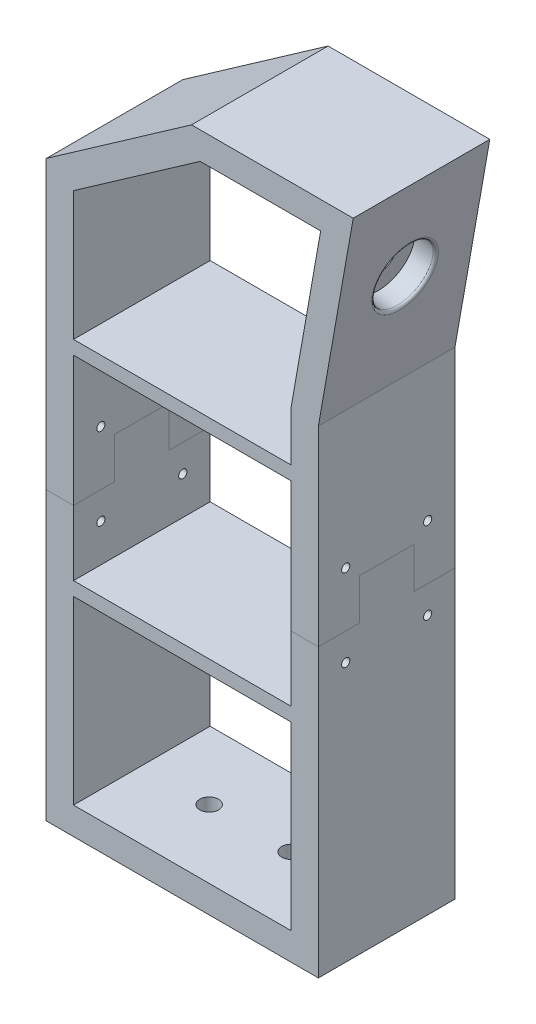
SolidWorks part; units mm, degrees
ref_plane "Front Plane" through (0, 0, 0) normal (0, 0, 1) x (1, 0, 0)
ref_plane "Top Plane" through (0, 0, 0) normal (0, 1, 0) x (1, 0, 0)
ref_plane "Right Plane" through (0, 0, 0) normal (1, 0, 0) x (0, 0, -1)
sketch "Sketch2" plane through (0, 0, 0) normal (0, 0, 1) x (1, 0, 0)
  line L8 (-40.5065, 0) -> (59.131, 0)
  line L12 (59.131, 0) -> (59.131, 175)
  line L14 (59.131, 175) -> (59.131, 265.8716) construction
  line L16 (49.131, 175.8749) -> (59.9525, 237.2467)
  line L17 (59.9525, 237.2467) -> (15.8403, 237.2467)
  line L18 (15.8403, 237.2467) -> (-30.5065, 204.7943)
  line L19 (0, 0) -> (0, 10) construction
  line L23 (-40.5065, 210) -> (-40.5065, 0)
  line L30 (59.131, 175) -> (71.87, 247.2467)
  line L35 (-30.5065, 204.7943) -> (-30.5065, 10)
  line L36 (71.87, 247.2467) -> (12.6873, 247.2467)
  line L37 (12.6873, 247.2467) -> (-40.5065, 210)
  line L38 (-30.5065, 10) -> (49.131, 10)
  line L39 (49.131, 10) -> (49.131, 175.8749)
  point P1 (9.131, 107.9897)
  dimension "D1" = 10
  dimension "D2" = 9.131
  dimension "D3" = 175
  dimension "D4" = 59.131
  dimension "D5" = 71.87
  dimension "D6" = 235
  dimension "D7" = 40.5065
  dimension "D8" = 210
  dimension "D9" = 10
extrude "Boss-Extrude1" add sketch "Sketch2" along normal blind 50
sketch "Sketch10" plane through (0, 10, 0) normal (0, 1, 0) x (1, 0, 0)
  line L0 (49.131, -25) -> (24.131, -25) construction
  line L1 (-30.869, -50) -> (-30.869, 0) construction
  line L2 (-30.5065, -50) -> (-30.5065, 0) construction
  line L3 (-30.5065, -25) -> (-5.8513, -25) construction
  line L5 (49.131, -50) -> (49.131, 0) construction
  circle A0 centre (-5.8513, -25) radius 3.425
  circle A1 centre (24.131, -25) radius 3.425
  dimension "D1" = 6.85
  dimension "D2" = 6.85
  dimension "D3" = 25.0177
  dimension "D4" = 55
extrude "Cut-Extrude5" cut sketch "Sketch10" against normal blind 10
sketch "Sketch11" plane through (0, 0, 50) normal (0, 0, 1) x (1, 0, 0)
  line L1 (-30.5065, 157.6357) -> (49.131, 157.6357)
  line L6 (-30.5065, 204.7943) -> (-30.5065, 10) construction
  line L7 (-30.5065, 81.1513) -> (-30.5065, 157.6357) construction
  line L9 (49.131, 157.6357) -> (49.131, 152.6357)
  line L10 (49.131, 152.6357) -> (-30.5065, 152.6357)
  line L11 (-30.5065, 152.6357) -> (-30.5065, 157.6357)
  line L12 (-30.5065, 81.1513) -> (49.131, 81.1513)
  line L13 (49.131, 81.1513) -> (49.131, 76.1513)
  line L14 (49.131, 76.1513) -> (-30.5065, 76.1513)
  line L15 (-30.5065, 76.1513) -> (-30.5065, 81.1513)
  line L16 (49.131, 10) -> (49.131, 175.8749) construction
  line L17 (-40.5065, 0) -> (59.131, 0) construction
  dimension "D1" = 5
  dimension "D2" = 5
  dimension "D3" = 76.1513
  dimension "D4" = 152.6357
extrude "Boss-Extrude3" add sketch "Sketch11" against normal blind 50
sketch "Sketch14" plane through (27.4212, -4.8351, 0) normal (0.9848, -0.1736, 0) x (0, 0, -1)
  line L0 (-25, 182.6093) -> (-25, 221.6093) construction
  line L1 (-50, 182.6093) -> (0, 182.6093) construction
  circle A0 centre (-25, 221.6093) radius 11.025
  dimension "D1" = 22.05
extrude "Cut-Extrude6" cut sketch "Sketch14" against normal blind 8
sketch "Sketch15" plane through (19.5427, -3.4459, 0) normal (0.9848, -0.1736, 0) x (0, 0, -1)
  line L0 (-25, 232.6343) -> (-25, 210.5843) construction
  circle A0 centre (-25, 221.6093) radius 11.025 construction
  circle A1 centre (-25, 221.6093) radius 4.05
  dimension "D1" = 8.1
extrude "Cut-Extrude7" cut sketch "Sketch15" against normal blind 3
fillet "Fillet1" radius 1 1 edges at (67.8177, 224.265, 25)
sketch "Sketch16" plane through (-40.5065, 0, 0) normal (-1, 0, 0) x (0, 0, 1)
  line L0 (0, 0) -> (0, 105) construction
  line L1 (0, 210) -> (0, 0) construction
  line L2 (0, 105) -> (50, 105) construction
  line L3 (50, 210) -> (50, 0) construction
  line L4 (50, 105) -> (50, 125) construction
  line L5 (50, 125) -> (40, 125) construction
  line L6 (50, 105) -> (50, 95) construction
  line L7 (50, 95) -> (40, 95) construction
  line L8 (25, 0) -> (25, 39.0827) construction
  line L9 (50, 0) -> (0, 0) construction
  circle A0 centre (40, 125) radius 1.5
  circle A1 centre (40, 95) radius 1.5
  circle A2 centre (10, 95) radius 1.5
  circle A3 centre (10, 125) radius 1.5
  dimension "D1" = 3
  dimension "D2" = 3
  dimension "D5" = 15
  dimension "D3" = 95
  dimension "D4" = 125
extrude "Cut-Extrude8" cut sketch "Sketch16" against normal through all
sketch "Sketch17" plane through (-40.5065, 0, 0) normal (-1, 0, 0) x (0, 0, 1)
  line L0 (0, 0) -> (0, 105) construction
  line L1 (0, 210) -> (0, 0) construction
  line L2 (0, 105) -> (15, 105)
  line L3 (15, 105) -> (15, 120)
  line L4 (15, 120) -> (35, 120)
  line L5 (35, 120) -> (35, 105)
  line L6 (35, 105) -> (50, 105)
  line L7 (50, 210) -> (50, 0) construction
  line L8 (50, 0) -> (0, 0) construction
  dimension "D1" = 105
  dimension "D2" = 120
  dimension "D3" = 15
  dimension "D4" = 15
split "Split1" trim tools "Sketch17" bodies to split 111 resulting bodies 112 113
